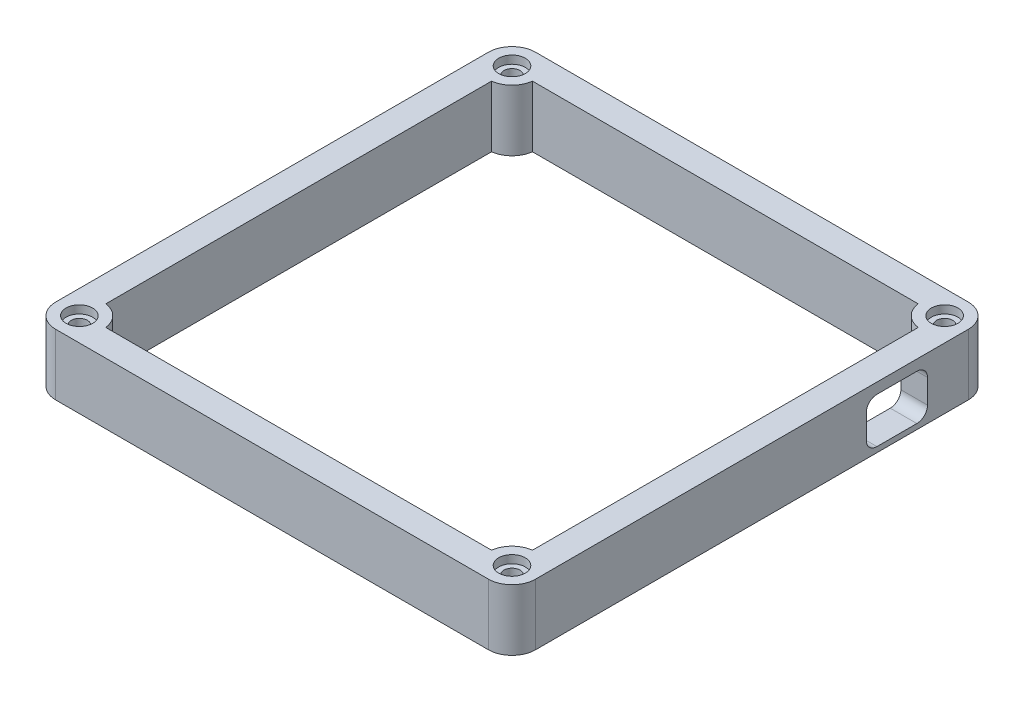
SolidWorks part; units mm, degrees
ref_plane "Front Plane" through (0, 0, 0) normal (0, 0, 1) x (1, 0, 0)
ref_plane "Top Plane" through (0, 0, 0) normal (0, 1, 0) x (1, 0, 0)
ref_plane "Right Plane" through (0, 0, 0) normal (1, 0, 0) x (0, 0, -1)
sketch "Sketch1" plane through (0, 0, 0) normal (0, 1, 0) x (1, 0, 0)
  line L0 (0, 0) -> (0, 40.64)
  line L1 (0, 40.64) -> (40.64, 40.64)
  line L2 (40.64, 40.64) -> (40.64, -40.64)
  line L3 (40.64, -40.64) -> (-40.64, -40.64)
  line L4 (-40.64, -40.64) -> (-40.64, 40.64)
  line L5 (-40.64, 40.64) -> (0, 40.64)
  line L6 (-40.64, -45.0809) -> (40.64, -45.0809)
  line L7 (-45.0809, -40.64) -> (-45.0809, 40.64)
  line L8 (-40.64, 45.0809) -> (40.64, 45.0809)
  line L9 (45.0809, 40.64) -> (45.0809, -40.64)
  line L10 (-45.0809, 18.4234) -> (-40.0809, 18.4234)
  line L11 (-7.938, 45.0809) -> (-7.938, 40.0809)
  line L12 (45.0809, 28.2685) -> (40.0809, 28.2685)
  line L13 (27.0858, -45.0809) -> (27.0858, -40.0809)
  line L14 (27.0858, -40.0809) -> (36.2345, -40.0809)
  line L15 (36.2345, -40.0809) -> (-36.2345, -40.0809)
  line L16 (-40.0809, 18.4234) -> (-40.0809, 36.2345)
  line L17 (-40.0809, 36.2345) -> (-40.0809, -36.2345)
  line L18 (-7.938, 40.0809) -> (-36.2345, 40.0809)
  line L19 (-36.2345, 40.0809) -> (36.2345, 40.0809)
  line L20 (40.0809, 28.2685) -> (40.0809, 36.2345)
  line L21 (40.0809, 36.2345) -> (40.0809, -36.2345)
  arc A0 (40.64, 45.0809) -> (45.0809, 40.64) centre (40.64, 40.64) cw
  arc A1 (-40.64, 45.0809) -> (-45.0809, 40.64) centre (-40.64, 40.64) ccw
  arc A2 (-45.0809, -40.64) -> (-40.64, -45.0809) centre (-40.64, -40.64) ccw
  arc A3 (45.0809, -40.64) -> (40.64, -45.0809) centre (40.64, -40.64) cw
  circle A4 centre (40.64, 40.64) radius 4.4409
  circle A5 centre (-40.64, 40.64) radius 4.4409
  circle A6 centre (-40.64, -40.64) radius 4.4409
  circle A7 centre (40.64, -40.64) radius 4.4409
extrude "Boss-Extrude1" add sketch "Sketch1" along normal blind 11.5 contours A6 L17 L10 L4 | A5 L4 L10 L16 | A5 L18 L11 L5 | A4 L1 L0 L19 | L11 L19 L0 L5 | A4 L20 L12 L2 | A7 L2 L12 L21 | L2 A7 L3 | A7 L14 L13 L3 | A6 L3 L13 L15 | A2 A6 L3 L4 | L3 A6 L4 | A6 L6 L13 L3 | A6 L4 L10 L7 | A3 A7 L2 L3 | A7 L3 L13 L6 | A7 L9 L12 L2 | A4 L2 L12 L9 | L2 A4 A0 L1 | L1 A4 L2 | A4 L8 L11 L5 L1 | A5 L5 L11 L8 | L5 A5 A1 L4 | L4 A5 L5 | A5 L7 L10 L4
sketch "Sketch2" plane through (0, 11.5, 0) normal (0, 1, 0) x (1, 0, 0)
  circle A0 centre (-40.64, 40.64) radius 1.5
  circle A1 centre (40.64, 40.64) radius 1.5
  circle A3 centre (40.64, -40.64) radius 1.5
  circle A4 centre (-40.64, -40.64) radius 1.5
extrude "Cut-Extrude1" cut sketch "Sketch2" against normal blind 8
sketch "Sketch3" plane through (45.0809, 0, 0) normal (1, 0, 0) x (0, 0, -1)
  line L0 (40.64, 11.5) -> (40.64, 0) construction
  line L1 (40.64, 11.5) -> (40.64, 0)
  line L2 (40.64, 11.5) -> (27.229, 11.5)
  line L3 (40.64, 11.5) -> (-40.64, 11.5) construction
  line L4 (27.229, 11.5) -> (27.229, 9.5)
  line L5 (28.6092, 11.5) -> (28.6092, 1)
  line L6 (27.229, 9.5) -> (32.979, 9.5)
  line L7 (32.979, 9.5) -> (32.979, 1)
  line L8 (32.979, 1) -> (27.229, 1)
  line L9 (27.229, 1) -> (21.479, 1)
  line L10 (21.479, 1) -> (21.479, 9.5)
  line L11 (21.479, 9.5) -> (27.229, 9.5)
  line L12 (32.979, 9.5) -> (32.979, 7.5)
  line L13 (32.979, 7.5) -> (30.979, 7.5)
  line L14 (32.979, 1) -> (32.979, 3)
  line L15 (32.979, 3) -> (30.979, 3)
  line L16 (21.479, 1) -> (23.479, 1)
  line L17 (23.479, 1) -> (23.479, 3)
  line L18 (21.479, 9.5) -> (23.479, 9.5)
  line L19 (23.479, 9.5) -> (23.479, 7.5)
  arc A0 (32.979, 7.5) -> (30.979, 9.5) centre (30.979, 7.5) ccw
  arc A1 (32.979, 3) -> (30.979, 1) centre (30.979, 3) cw
  arc A2 (23.479, 1) -> (21.479, 3) centre (23.479, 3) cw
  arc A3 (23.479, 9.5) -> (21.479, 7.5) centre (23.479, 7.5) ccw
extrude "Cut-Extrude2" cut sketch "Sketch3" against normal blind 8
sketch "Sketch4" plane through (0, 11.5, 0) normal (0, 1, 0) x (1, 0, 0)
  circle A0 centre (-40.64, 40.64) radius 2.5
  circle A1 centre (40.64, 40.64) radius 2.5
  circle A2 centre (40.64, -40.64) radius 2.5
  circle A3 centre (-40.64, -40.64) radius 2.5
extrude "Cut-Extrude3" cut sketch "Sketch4" against normal blind 1.5
